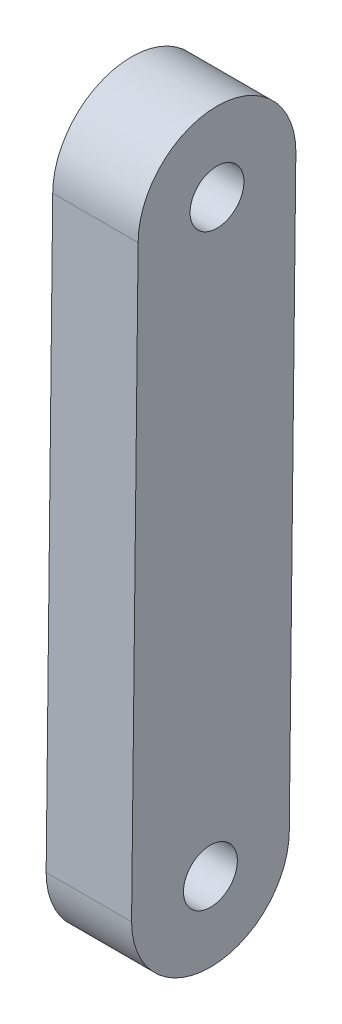
SolidWorks part; units mm, degrees
ref_plane "Front Plane" through (0, 0, 0) normal (0, 0, 1) x (1, 0, 0)
ref_plane "Top Plane" through (0, 0, 0) normal (0, 1, 0) x (1, 0, 0)
ref_plane "Right Plane" through (0, 0, 0) normal (1, 0, 0) x (0, 0, -1)
sketch "Sketch1" plane through (-14.5, 0, 0) normal (1, 0, 0) x (0, 0, -1)
  line L0 (-29.5, -136.5) -> (-30, -181)
  line L1 (-17.5, -136.5) -> (-18, -181)
  arc A0 (-30, -181) -> (-18, -181) centre (-24, -181) ccw
  arc A1 (-17.5, -136.5) -> (-29.5, -136.5) centre (-23.5, -136.5) ccw
  circle A2 centre (-24, -181) radius 2.05 construction
  circle A3 centre (-23.5, -136.5) radius 2.05 construction
  circle A4 centre (-24, -181) radius 2.05
  circle A5 centre (-23.5, -136.5) radius 2.05
  line M8 (-13.6015, -175.5) -> (-24, -175.5)
  arc M9 (-24, -175.5) -> (-24, -186.5) centre (-24, -181) ccw
  line M10 (-24, -186.5) -> (-13.6015, -186.5)
  circle M19 centre (-24, -181) radius 2.05
  dimension "D1" = 12
  dimension "D2" = 12
extrude "Boss-Extrude1" add sketch "Sketch1" along normal up to surface (6.5 mm away) contours L1 A1 L0 A0 A5 M10 M9 M8 | A0 L1 M10 M8 M9 M19
